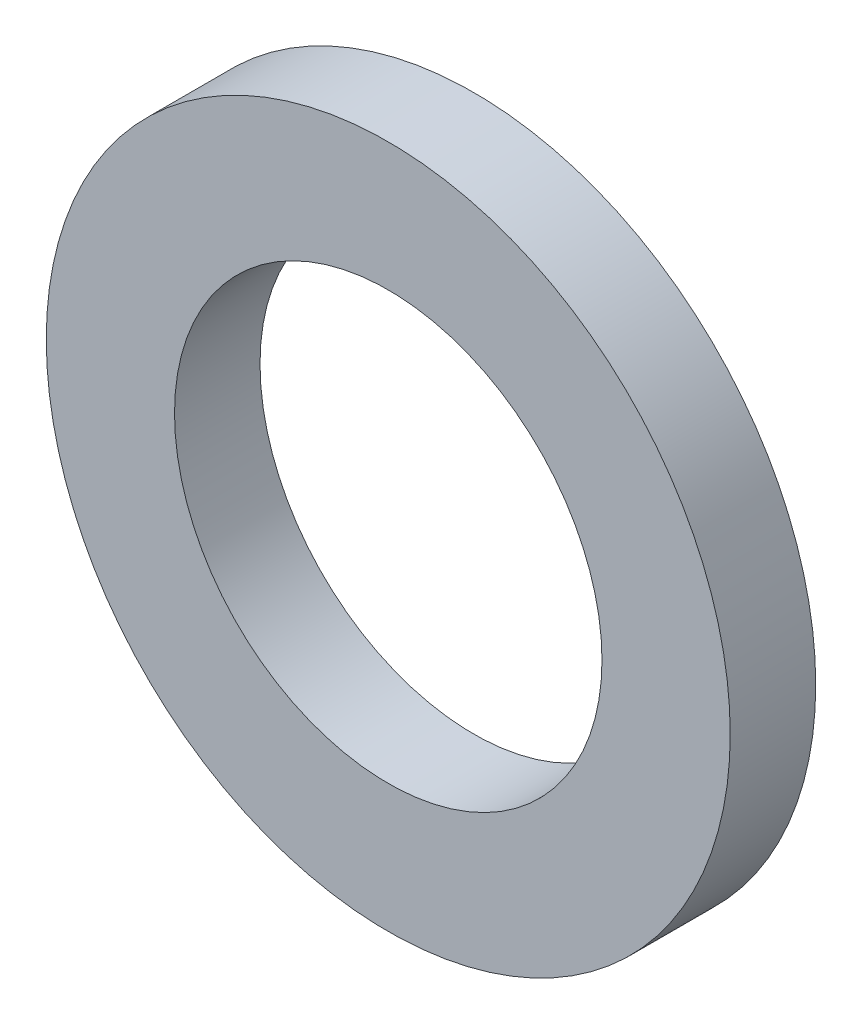
SolidWorks part; units mm, degrees
ref_plane "Front Plane" through (0, 0, 0) normal (0, 0, 1) x (1, 0, 0)
ref_plane "Top Plane" through (0, 0, 0) normal (0, 1, 0) x (1, 0, 0)
ref_plane "Right Plane" through (0, 0, 0) normal (1, 0, 0) x (0, 0, -1)
sketch "Sketch1" plane through (0, 0, 0) normal (0, 0, 1) x (1, 0, 0)
  circle A0 centre (0, 0) radius 2.5
  circle A1 centre (0, 0) radius 4
  dimension "D1" = 8
  dimension "D2" = 5
extrude "Boss-Extrude1" add sketch "Sketch1" along normal blind 1
